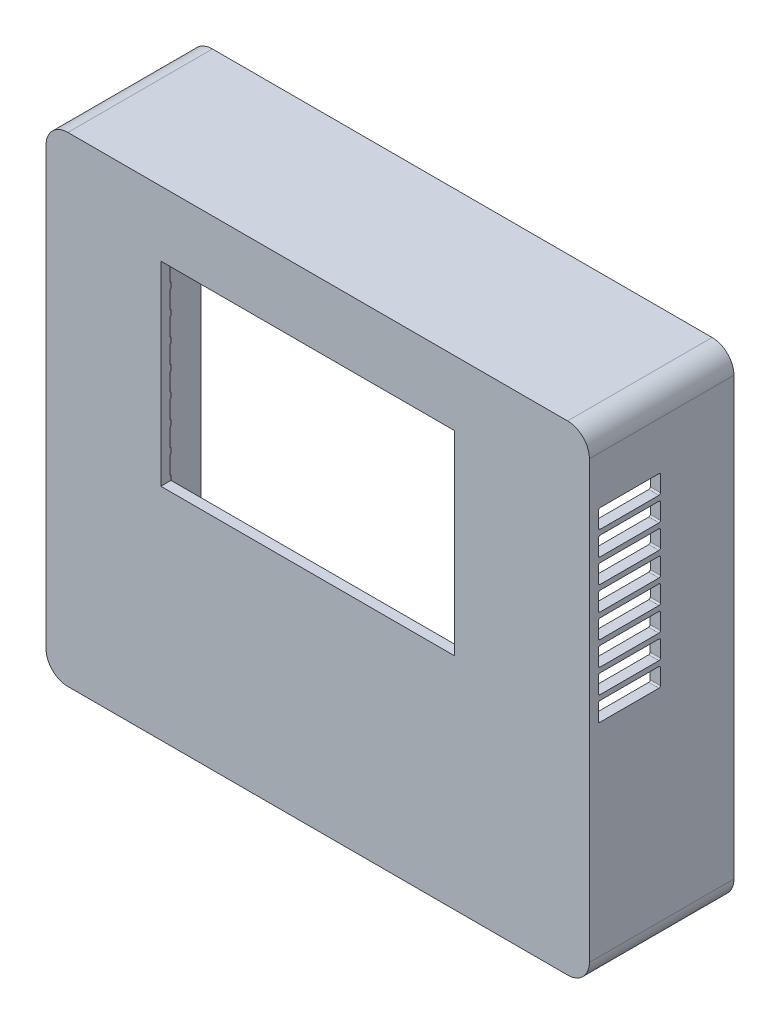
SolidWorks part; units mm, degrees
ref_plane "Front Plane" through (0, 0, 0) normal (0, 0, 1) x (1, 0, 0)
ref_plane "Top Plane" through (0, 0, 0) normal (0, 1, 0) x (1, 0, 0)
ref_plane "Right Plane" through (0, 0, 0) normal (1, 0, 0) x (0, 0, -1)
sketch "Sketch1" plane through (0, 0, 0) normal (0, 0, 1) x (1, 0, 0)
  line L4 (84, 51.09) -> (-14.4, 51.09)
  line L5 (-18.7, 46.79) -> (-18.7, -39.11)
  line L6 (-14.4, -43.41) -> (84, -43.41)
  line L7 (88.3, -39.11) -> (88.3, 46.79)
  line L8 (84, 51.09) -> (-14.4, 51.09)
  line L9 (-18.7, 46.79) -> (-18.7, -39.11)
  line L10 (-14.4, -43.41) -> (84, -43.41)
  line L11 (88.3, -39.11) -> (88.3, 46.79)
  line L12 (61.7, -0.1) -> (61.7, 38.3)
  line L13 (61.7, 38.3) -> (3.9, 38.3)
  line L14 (3.9, 38.3) -> (3.9, -0.1)
  line L15 (3.9, -0.1) -> (61.7, -0.1)
  line L16 (61.7, -0.1) -> (61.7, 38.3)
  line L17 (61.7, 38.3) -> (3.9, 38.3)
  line L18 (3.9, 38.3) -> (3.9, -0.1)
  line L19 (3.9, -0.1) -> (61.7, -0.1)
  arc A4 (88.3, 46.79) -> (84, 51.09) centre (84, 46.79) ccw
  arc A5 (-14.4, 51.09) -> (-18.7, 46.79) centre (-14.4, 46.79) ccw
  arc A6 (-18.7, -39.11) -> (-14.4, -43.41) centre (-14.4, -39.11) ccw
  arc A7 (84, -43.41) -> (88.3, -39.11) centre (84, -39.11) ccw
  arc A8 (88.3, 46.79) -> (84, 51.09) centre (84, 46.79) ccw
  arc A9 (-14.4, 51.09) -> (-18.7, 46.79) centre (-14.4, 46.79) ccw
  arc A10 (-18.7, -39.11) -> (-14.4, -43.41) centre (-14.4, -39.11) ccw
  arc A11 (84, -43.41) -> (88.3, -39.11) centre (84, -39.11) ccw
  dimension "D1" = 0
  dimension "D2" = 0
extrude "Boss-Extrude3" add sketch "Sketch1" against normal blind 2
sketch "Sketch3" plane through (0, 0, 0) normal (0, 0, 1) x (1, 0, 0)
  line L4 (84, 51.09) -> (-14.4, 51.09)
  line L5 (-18.7, 46.79) -> (-18.7, -39.11)
  line L6 (-14.4, -43.41) -> (84, -43.41)
  line L7 (88.3, -39.11) -> (88.3, 46.79)
  line L8 (84, 51.09) -> (-14.4, 51.09)
  line L9 (-18.7, 46.79) -> (-18.7, -39.11)
  line L10 (-14.4, -43.41) -> (84, -43.41)
  line L11 (88.3, -39.11) -> (88.3, 46.79)
  line L20 (84, 49.09) -> (-14.4, 49.09)
  line L21 (-16.7, 46.79) -> (-16.7, -39.11)
  line L22 (-14.4, -41.41) -> (84, -41.41)
  line L23 (86.3, -39.11) -> (86.3, 46.79)
  line L24 (84, 49.09) -> (-14.4, 49.09)
  line L25 (-16.7, 46.79) -> (-16.7, -39.11)
  line L26 (-14.4, -41.41) -> (84, -41.41)
  line L27 (86.3, -39.11) -> (86.3, 46.79)
  arc A4 (88.3, 46.79) -> (84, 51.09) centre (84, 46.79) ccw
  arc A5 (-14.4, 51.09) -> (-18.7, 46.79) centre (-14.4, 46.79) ccw
  arc A6 (-18.7, -39.11) -> (-14.4, -43.41) centre (-14.4, -39.11) ccw
  arc A7 (84, -43.41) -> (88.3, -39.11) centre (84, -39.11) ccw
  arc A8 (88.3, 46.79) -> (84, 51.09) centre (84, 46.79) ccw
  arc A9 (-14.4, 51.09) -> (-18.7, 46.79) centre (-14.4, 46.79) ccw
  arc A10 (-18.7, -39.11) -> (-14.4, -43.41) centre (-14.4, -39.11) ccw
  arc A11 (84, -43.41) -> (88.3, -39.11) centre (84, -39.11) ccw
  arc A20 (86.3, 46.79) -> (84, 49.09) centre (84, 46.79) ccw
  arc A21 (-14.4, 49.09) -> (-16.7, 46.79) centre (-14.4, 46.79) ccw
  arc A22 (-16.7, -39.11) -> (-14.4, -41.41) centre (-14.4, -39.11) ccw
  arc A23 (84, -41.41) -> (86.3, -39.11) centre (84, -39.11) ccw
  arc A24 (86.3, 46.79) -> (84, 49.09) centre (84, 46.79) ccw
  arc A25 (-14.4, 49.09) -> (-16.7, 46.79) centre (-14.4, 46.79) ccw
  arc A26 (-16.7, -39.11) -> (-14.4, -41.41) centre (-14.4, -39.11) ccw
  arc A27 (84, -41.41) -> (86.3, -39.11) centre (84, -39.11) ccw
  dimension "D1" = 0
  dimension "D2" = 2
extrude "Boss-Extrude4" add sketch "Sketch3" against normal up to surface (28.466 mm away)
sketch "Sketch5" plane through (0, -43.41, 0) normal (0, -1, 0) x (1, 0, 0)
  line L0 (72.33, -24.7898) -> (72.33, -28.2198) construction
  line L1 (72.33, -28.2198) -> (81.22, -28.2198) construction
  line L2 (81.22, -28.2198) -> (81.22, -24.7898) construction
  line L3 (81.22, -24.7898) -> (72.33, -24.7898) construction
  line L4 (84, 0) -> (-14.4, 0)
  line L5 (-14.4, 0) -> (-14.4, -28.466)
  line L6 (-14.4, -28.466) -> (84, -28.466)
  line L7 (84, -28.466) -> (84, 0)
  line L8 (84, 0) -> (-14.4, 0)
  line L9 (-14.4, 0) -> (-14.4, -28.466)
  line L10 (-14.4, -28.466) -> (84, -28.466)
  line L11 (84, -28.466) -> (84, 0)
  line L12 (-13.85, -17.296) -> (-13.85, -28.296)
  line L13 (-13.85, -28.296) -> (-4.55, -28.296)
  line L14 (-4.55, -28.296) -> (-4.55, -17.296)
  line L15 (-4.55, -17.296) -> (-13.85, -17.296)
  line L16 (-13.85, -17.296) -> (-13.85, -28.296)
  line L17 (-13.85, -28.296) -> (-4.55, -28.296)
  line L18 (-4.55, -28.296) -> (-4.55, -17.296)
  line L19 (-4.55, -17.296) -> (-13.85, -17.296)
  line L20 (20.375, -11.3798) -> (20.375, -28.2198)
  line L21 (20.375, -28.2198) -> (34.425, -28.2198)
  line L22 (34.425, -28.2198) -> (34.425, -11.3798)
  line L23 (34.425, -11.3798) -> (20.375, -11.3798)
  line L24 (20.375, -11.3798) -> (20.375, -28.2198)
  line L25 (20.375, -28.2198) -> (34.425, -28.2198)
  line L26 (34.425, -28.2198) -> (34.425, -11.3798)
  line L27 (34.425, -11.3798) -> (20.375, -11.3798)
  line L28 (68.12, -28.296) -> (69.827, -28.296) construction
  line L29 (69.827, -28.296) -> (69.827, -14.646) construction
  line L30 (69.827, -14.646) -> (68.12, -14.646) construction
  line L31 (66.12, -28.296) -> (68.12, -28.296) construction
  line L32 (68.12, -14.646) -> (66.12, -14.646) construction
  line L33 (53.673, -14.646) -> (53.673, -28.296) construction
  line L34 (53.673, -28.296) -> (55.38, -28.296) construction
  line L35 (55.38, -14.646) -> (53.673, -14.646) construction
  line L36 (55.38, -28.296) -> (57.38, -28.296) construction
  line L37 (57.38, -14.646) -> (55.38, -14.646) construction
  line L38 (57.38, -28.296) -> (66.12, -28.296) construction
  line L39 (66.12, -14.646) -> (57.38, -14.646) construction
  line L40 (37.375, -11.3798) -> (37.375, -28.2198) construction
  line L41 (37.375, -28.2198) -> (51.425, -28.2198) construction
  line L42 (51.425, -28.2198) -> (51.425, -11.3798) construction
  line L43 (51.425, -11.3798) -> (37.375, -11.3798) construction
  line L44 (20.375, -11.3798) -> (20.375, -28.2198) construction
  line L45 (20.375, -28.2198) -> (34.425, -28.2198) construction
  line L46 (34.425, -28.2198) -> (34.425, -11.3798) construction
  line L47 (34.425, -11.3798) -> (20.375, -11.3798) construction
  line L48 (-1.288, -21.4098) -> (-1.288, -28.2198) construction
  line L49 (-1.288, -28.2198) -> (16.408, -28.2198) construction
  line L50 (16.408, -28.2198) -> (16.408, -21.4098) construction
  line L51 (16.408, -21.4098) -> (-1.288, -21.4098) construction
  line L52 (-13.85, -17.296) -> (-13.85, -28.296) construction
  line L53 (-13.85, -28.296) -> (-4.55, -28.296) construction
  line L54 (-4.55, -28.296) -> (-4.55, -17.296) construction
  line L55 (-4.55, -17.296) -> (-13.85, -17.296) construction
  line L56 (72.33, -24.7898) -> (72.33, -28.2198)
  line L57 (72.33, -28.2198) -> (81.22, -28.2198)
  line L58 (81.22, -28.2198) -> (81.22, -24.7898)
  line L59 (81.22, -24.7898) -> (72.33, -24.7898)
  line L60 (68.12, -28.296) -> (69.827, -28.296)
  line L61 (69.827, -28.296) -> (69.827, -14.646)
  line L62 (69.827, -14.646) -> (68.12, -14.646)
  line L63 (66.12, -28.296) -> (68.12, -28.296)
  line L64 (68.12, -14.646) -> (66.12, -14.646)
  line L65 (53.673, -14.646) -> (53.673, -28.296)
  line L66 (53.673, -28.296) -> (55.38, -28.296)
  line L67 (55.38, -14.646) -> (53.673, -14.646)
  line L68 (55.38, -28.296) -> (57.38, -28.296)
  line L69 (57.38, -14.646) -> (55.38, -14.646)
  line L70 (57.38, -28.296) -> (66.12, -28.296)
  line L71 (66.12, -14.646) -> (57.38, -14.646)
  line L72 (37.375, -11.3798) -> (37.375, -28.2198)
  line L73 (37.375, -28.2198) -> (51.425, -28.2198)
  line L74 (51.425, -28.2198) -> (51.425, -11.3798)
  line L75 (51.425, -11.3798) -> (37.375, -11.3798)
  line L76 (20.375, -11.3798) -> (20.375, -28.2198)
  line L77 (20.375, -28.2198) -> (34.425, -28.2198)
  line L78 (34.425, -28.2198) -> (34.425, -11.3798)
  line L79 (34.425, -11.3798) -> (20.375, -11.3798)
  line L80 (-1.288, -21.4098) -> (-1.288, -28.2198)
  line L81 (-1.288, -28.2198) -> (16.408, -28.2198)
  line L82 (16.408, -28.2198) -> (16.408, -21.4098)
  line L83 (16.408, -21.4098) -> (-1.288, -21.4098)
  line L84 (-13.85, -17.296) -> (-13.85, -28.296)
  line L85 (-13.85, -28.296) -> (-4.55, -28.296)
  line L86 (-4.55, -28.296) -> (-4.55, -17.296)
  line L87 (-4.55, -17.296) -> (-13.85, -17.296)
  dimension "D1" = 0
  dimension "D2" = 0
  dimension "D3" = 0
extrude "Cut-Extrude1" cut sketch "Sketch5" against normal blind 2 contours L18 L19 L16 L17 | L82 L83 L80 L81 | L26 L27 L24 L25 | L74 L75 L72 L73 | L64 L71 L69 L67 L65 L66 L68 L70 L63 L60 L61 L62 | L58 L59 L56 L57
sketch "Sketch6" plane through (-18.7, 0, 0) normal (-1, 0, 0) x (0, 0, 1)
  line L1 (-1.8, 34) -> (-1.8, 37.1) construction
  line L2 (-13.7, 33.7) -> (-2.1, 33.7) construction
  line L3 (-14, 37.1) -> (-14, 34) construction
  line L12 (-2.1, 37.4) -> (-13.7, 37.4) construction
  line L13 (-1.8, 34) -> (-1.8, 37.1)
  line L14 (-13.7, 33.7) -> (-2.1, 33.7)
  line L15 (-14, 37.1) -> (-14, 34)
  line L16 (-2.1, 37.4) -> (-13.7, 37.4)
  line L17 (-1.7965, 29.3019) -> (-1.7965, 32.4019)
  line L18 (-13.6965, 29.0019) -> (-2.0965, 29.0019)
  line L19 (-13.9965, 32.4019) -> (-13.9965, 29.3019)
  line L20 (-2.0965, 32.7019) -> (-13.6965, 32.7019)
  line L21 (-1.793, 24.6037) -> (-1.793, 27.7037)
  line L22 (-13.693, 24.3037) -> (-2.093, 24.3037)
  line L23 (-13.993, 27.7037) -> (-13.993, 24.6037)
  line L24 (-2.093, 28.0037) -> (-13.693, 28.0037)
  line L25 (-1.7895, 19.9056) -> (-1.7895, 23.0056)
  line L26 (-13.6895, 19.6056) -> (-2.0895, 19.6056)
  line L27 (-13.9895, 23.0056) -> (-13.9895, 19.9056)
  line L28 (-2.0895, 23.3056) -> (-13.6895, 23.3056)
  line L29 (-1.786, 15.2075) -> (-1.786, 18.3075)
  line L30 (-13.686, 14.9075) -> (-2.086, 14.9075)
  line L31 (-13.986, 18.3075) -> (-13.986, 15.2075)
  line L32 (-2.086, 18.6075) -> (-13.686, 18.6075)
  line L33 (-1.7825, 10.5094) -> (-1.7825, 13.6094)
  line L34 (-13.6825, 10.2094) -> (-2.0825, 10.2094)
  line L35 (-13.9825, 13.6094) -> (-13.9825, 10.5094)
  line L36 (-2.0825, 13.9094) -> (-13.6825, 13.9094)
  line L37 (-1.779, 5.8112) -> (-1.779, 8.9112)
  line L38 (-13.679, 5.5112) -> (-2.079, 5.5112)
  line L39 (-13.979, 8.9112) -> (-13.979, 5.8112)
  line L40 (-2.079, 9.2112) -> (-13.679, 9.2112)
  line L41 (-1.7755, 1.1131) -> (-1.7755, 4.2131)
  line L42 (-13.6755, 0.8131) -> (-2.0755, 0.8131)
  line L43 (-13.9755, 4.2131) -> (-13.9755, 1.1131)
  line L44 (-2.0755, 4.5131) -> (-13.6755, 4.5131)
  arc A1 (-2.1, 33.7) -> (-1.8, 34) centre (-2.1, 34) ccw construction
  arc A2 (-1.8, 37.1) -> (-2.1, 37.4) centre (-2.1, 37.1) ccw construction
  arc A3 (-14, 34) -> (-13.7, 33.7) centre (-13.7, 34) ccw construction
  arc A4 (-13.7, 37.4) -> (-14, 37.1) centre (-13.7, 37.1) ccw construction
  arc A5 (-2.1, 33.7) -> (-1.8, 34) centre (-2.1, 34) ccw
  arc A6 (-1.8, 37.1) -> (-2.1, 37.4) centre (-2.1, 37.1) ccw
  arc A7 (-14, 34) -> (-13.7, 33.7) centre (-13.7, 34) ccw
  arc A8 (-13.7, 37.4) -> (-14, 37.1) centre (-13.7, 37.1) ccw
  arc A9 (-2.0965, 29.0019) -> (-1.7965, 29.3019) centre (-2.0965, 29.3019) ccw
  arc A10 (-1.7965, 32.4019) -> (-2.0965, 32.7019) centre (-2.0965, 32.4019) ccw
  arc A11 (-13.9965, 29.3019) -> (-13.6965, 29.0019) centre (-13.6965, 29.3019) ccw
  arc A12 (-13.6965, 32.7019) -> (-13.9965, 32.4019) centre (-13.6965, 32.4019) ccw
  arc A13 (-2.093, 24.3037) -> (-1.793, 24.6037) centre (-2.093, 24.6037) ccw
  arc A14 (-1.793, 27.7037) -> (-2.093, 28.0037) centre (-2.093, 27.7037) ccw
  arc A15 (-13.993, 24.6037) -> (-13.693, 24.3037) centre (-13.693, 24.6037) ccw
  arc A16 (-13.693, 28.0037) -> (-13.993, 27.7037) centre (-13.693, 27.7037) ccw
  arc A17 (-2.0895, 19.6056) -> (-1.7895, 19.9056) centre (-2.0895, 19.9056) ccw
  arc A18 (-1.7895, 23.0056) -> (-2.0895, 23.3056) centre (-2.0895, 23.0056) ccw
  arc A19 (-13.9895, 19.9056) -> (-13.6895, 19.6056) centre (-13.6895, 19.9056) ccw
  arc A20 (-13.6895, 23.3056) -> (-13.9895, 23.0056) centre (-13.6895, 23.0056) ccw
  arc A21 (-2.086, 14.9075) -> (-1.786, 15.2075) centre (-2.086, 15.2075) ccw
  arc A22 (-1.786, 18.3075) -> (-2.086, 18.6075) centre (-2.086, 18.3075) ccw
  arc A23 (-13.986, 15.2075) -> (-13.686, 14.9075) centre (-13.686, 15.2075) ccw
  arc A24 (-13.686, 18.6075) -> (-13.986, 18.3075) centre (-13.686, 18.3075) ccw
  arc A25 (-2.0825, 10.2094) -> (-1.7825, 10.5094) centre (-2.0825, 10.5094) ccw
  arc A26 (-1.7825, 13.6094) -> (-2.0825, 13.9094) centre (-2.0825, 13.6094) ccw
  arc A27 (-13.9825, 10.5094) -> (-13.6825, 10.2094) centre (-13.6825, 10.5094) ccw
  arc A28 (-13.6825, 13.9094) -> (-13.9825, 13.6094) centre (-13.6825, 13.6094) ccw
  arc A29 (-2.079, 5.5112) -> (-1.779, 5.8112) centre (-2.079, 5.8112) ccw
  arc A30 (-1.779, 8.9112) -> (-2.079, 9.2112) centre (-2.079, 8.9112) ccw
  arc A31 (-13.979, 5.8112) -> (-13.679, 5.5112) centre (-13.679, 5.8112) ccw
  arc A32 (-13.679, 9.2112) -> (-13.979, 8.9112) centre (-13.679, 8.9112) ccw
  arc A33 (-2.0755, 0.8131) -> (-1.7755, 1.1131) centre (-2.0755, 1.1131) ccw
  arc A34 (-1.7755, 4.2131) -> (-2.0755, 4.5131) centre (-2.0755, 4.2131) ccw
  arc A35 (-13.9755, 1.1131) -> (-13.6755, 0.8131) centre (-13.6755, 1.1131) ccw
  arc A36 (-13.6755, 4.5131) -> (-13.9755, 4.2131) centre (-13.6755, 4.2131) ccw
  dimension "D2" = 8
extrude "Cut-Extrude2" cut sketch "Sketch6" against normal through all
